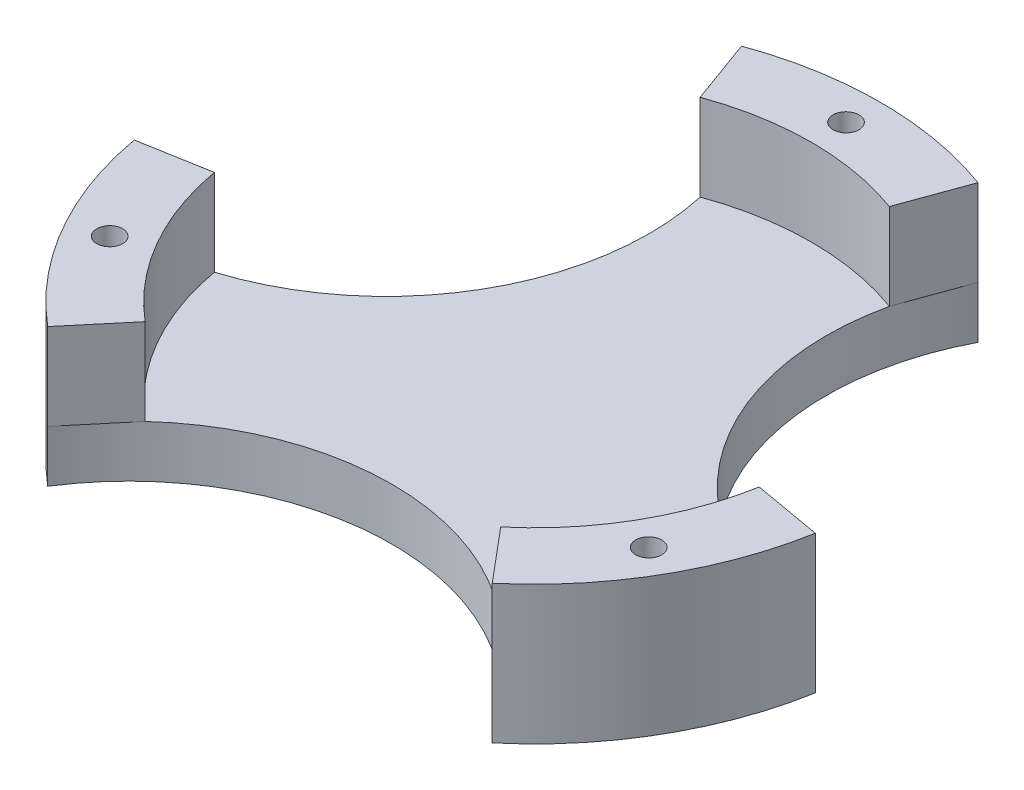
SolidWorks part; units mm, degrees
ref_plane "Front Plane" through (0, 0, 0) normal (0, 0, 1) x (1, 0, 0)
ref_plane "Top Plane" through (0, 0, 0) normal (0, 1, 0) x (1, 0, 0)
ref_plane "Right Plane" through (0, 0, 0) normal (1, 0, 0) x (0, 0, -1)
sketch "Sketch1" plane through (0, 0, 0) normal (0, 1, 0) x (1, 0, 0)
  circle A0 centre (0, 0) radius 40
  dimension "D1" = 80
extrude "Boss-Extrude1" add sketch "Sketch1" along normal blind 6
sketch "Sketch2" plane through (0, 6, 0) normal (0, 1, 0) x (1, 0, 0)
  line L0 (-13.6808, 37.5877) -> (0, 0) construction
  line L1 (0, 0) -> (13.6808, 37.5877) construction
  line L2 (0, -1000) -> (0, 49000) construction
  line L3 (-13.6808, 37.5877) -> (-10.9446, 30.0702)
  line L4 (10.9446, 30.0702) -> (13.6808, 37.5877)
  arc A0 (13.6808, 37.5877) -> (-13.6808, 37.5877) centre (0, 0) ccw
  circle A1 centre (0, 0) radius 40 construction
  arc A2 (10.9446, 30.0702) -> (-10.9446, 30.0702) centre (0, 0) ccw
  circle A3 centre (0, 36) radius 1.5
  dimension "D1" = 8
  dimension "D5" = 3
  dimension "D2" = 20
  dimension "D3" = 20
  dimension "D4" = 36
extrude "Boss-Extrude2" add sketch "Sketch2" along normal blind 10
sketch "Sketch16" plane through (0, 16, 0) normal (0, 1, 0) x (1, 0, 0)
  circle A0 centre (0, 36) radius 1.5
  circle A1 centre (0, 36) radius 1.5 construction
extrude "Cut-Extrude9" cut sketch "Sketch16" against normal through all
pattern_circular "CirPattern1" count 3 over 360 about axis through (0, 0, 0) along (0, 1, 0) of "Boss-Extrude2", "Cut-Extrude9"
sketch "Sketch5" plane through (0, 6, 0) normal (0, 1, 0) x (1, 0, 0)
  circle A1 centre (40.6986, 23.4973) radius 30.4713
extrude "Cut-Extrude3" cut sketch "Sketch5" against normal through all
pattern_circular "CirPattern2" count 3 over 360 about axis through (0, 0, 0) along (0, 1, 0) of "Cut-Extrude3"
